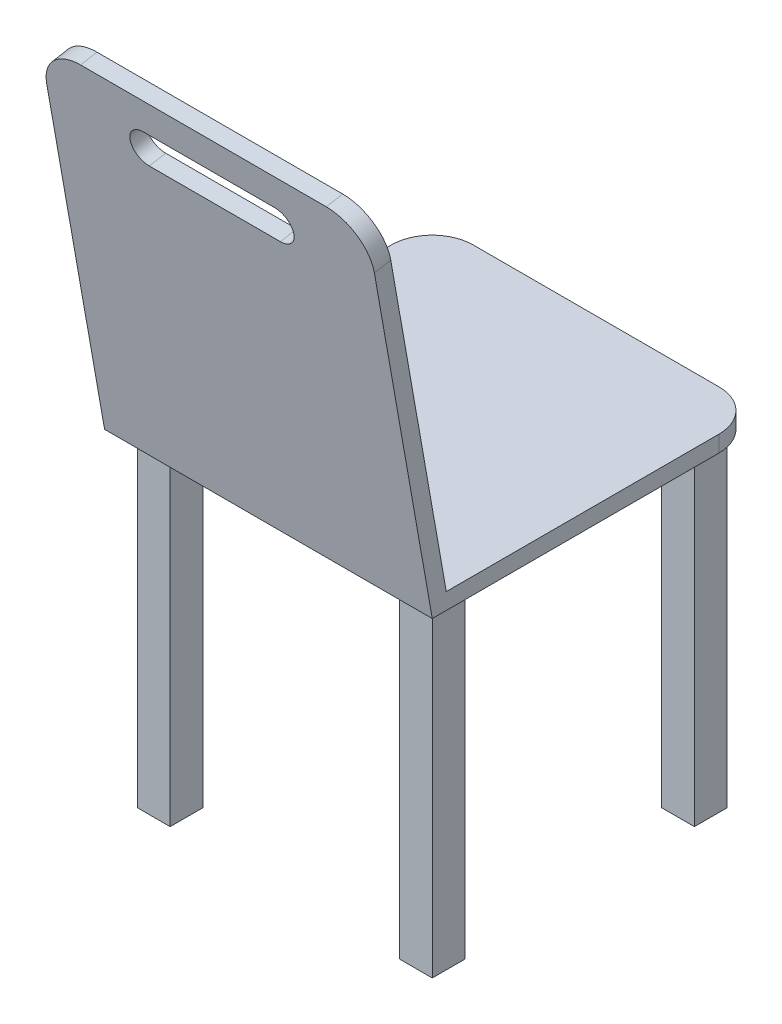
SolidWorks part; units mm, degrees
material "Oak"
ref_plane "Front Plane" through (0, 0, 0) normal (0, 0, 1) x (1, 0, 0)
ref_plane "Top Plane" through (0, 0, 0) normal (0, 1, 0) x (1, 0, 0)
ref_plane "Right Plane" through (0, 0, 0) normal (1, 0, 0) x (0, 0, -1)
sketch "Sketch1" plane through (0, 0, 0) normal (1, 0, 0) x (0, 0, -1)
  line L0 (0, 0) -> (-79.3471, 450)
  line L1 (-79.3471, 450) -> (-59.3471, 453.5265)
  line L2 (-59.3471, 453.5265) -> (17.0953, 20)
  line L3 (17.0953, 20) -> (400, 20)
  line L4 (0, 0) -> (400, 0)
  line L5 (400, 0) -> (400, 20)
  dimension "D1" = 100
  dimension "D2" = 20
  dimension "D3" = 20
  dimension "D4" = 400
  dimension "D5" = 450
extrude "Boss-Extrude1" add sketch "Sketch1" along normal blind 400
sketch "Sketch2" plane through (0, 0, 0) normal (0, 1, 0) x (1, 0, 0)
  line L0 (20, 20) -> (20, 60)
  line L1 (60, 60) -> (60, 20)
  line L2 (60, 20) -> (20, 20)
  line L3 (20, 60) -> (60, 60)
  line L4 (0, 0) -> (0, 400) construction
  line L5 (400, 0) -> (0, 0) construction
  line L6 (340, 20) -> (340, 60)
  line L7 (380, 60) -> (380, 20)
  line L8 (380, 20) -> (340, 20)
  line L9 (340, 60) -> (380, 60)
  line L10 (20, 340) -> (20, 380)
  line L11 (60, 380) -> (60, 340)
  line L12 (60, 340) -> (20, 340)
  line L13 (20, 380) -> (60, 380)
  line L14 (340, 340) -> (340, 380)
  line L15 (380, 380) -> (380, 340)
  line L16 (380, 340) -> (340, 340)
  line L17 (340, 380) -> (380, 380)
  line L18 (400, 400) -> (0, 400) construction
  line L19 (400, 0) -> (400, 400) construction
  point P24 (0, 0)
  dimension "D1" = 40
  dimension "D2" = 40
  dimension "D3" = 20
  dimension "D4" = 20
  dimension "D5" = 20
  dimension "D6" = 20
  dimension "D7" = 40
extrude "Boss-Extrude2" add sketch "Sketch2" against normal blind 400 contours L3 L1 L2 L0
sketch "Sketch3" plane through (0, 232.1276, 20.3085) normal (0, 0.1736, -0.9848) x (1, 0, 0)
  line L4 (280, -144.8144) -> (120, -144.8144)
  line L5 (280, -184.8144) -> (120, -184.8144)
  line L6 (400, -224.8144) -> (0, -224.8144) construction
  line L7 (0, 215.4) -> (0, -224.8144) construction
  arc A4 (280, -144.8144) -> (280, -184.8144) centre (280, -164.8144) cw
  arc A5 (120, -144.8144) -> (120, -184.8144) centre (120, -164.8144) ccw
  point P6 (300, -164.8144)
  point P7 (100, -164.8144)
  dimension "D3" = 40
  dimension "D1" = 200
  dimension "D2" = 40
  dimension "D4" = 100
extrude "Cut-Extrude2" cut sketch "Sketch3" against normal blind 360 contours L4 A5 L5 A4
fillet "Fillet2" radius 50 1 edges at (400, 451.7633, 69.3471)
fillet "Fillet3" radius 50 1 edges at (0, 451.7633, 69.3471)
fillet "Fillet4" radius 50 1 edges at (0, 10, -400)
fillet "Fillet5" radius 50 1 edges at (400, 10, -400)
